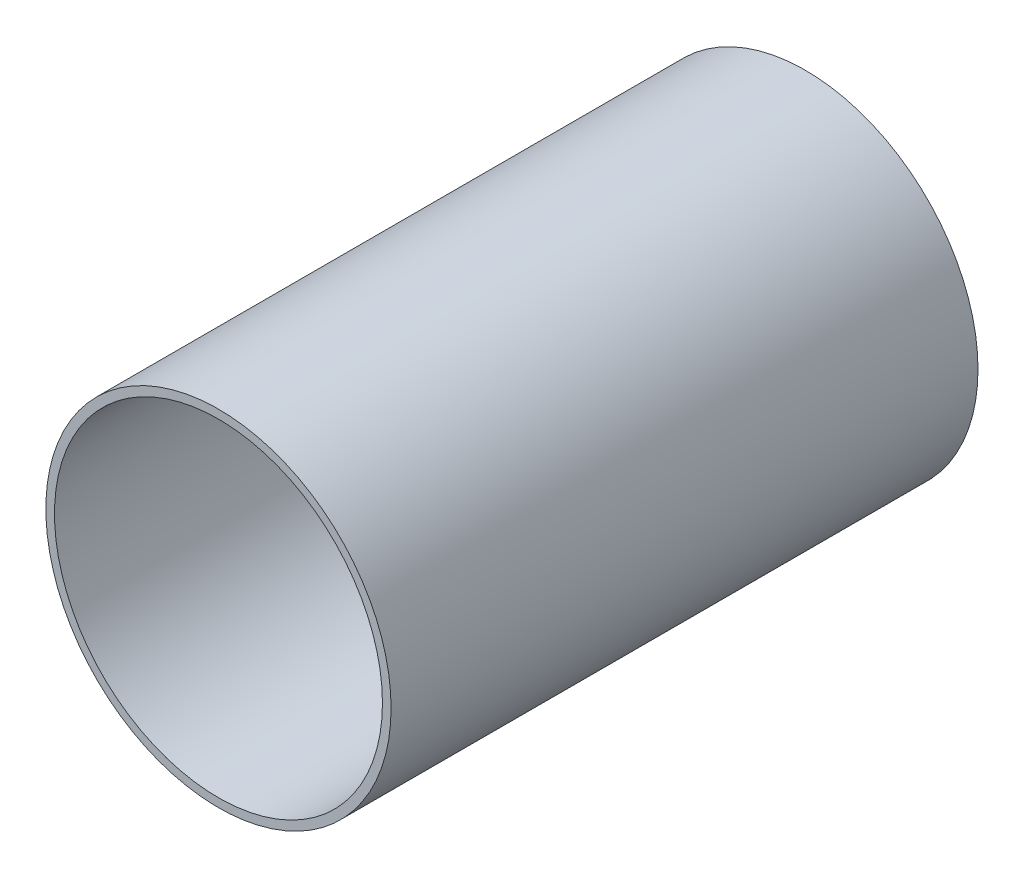
SolidWorks part; units mm, degrees
material "6061-T6 (SS)"
ref_plane "Front Plane" through (0, 0, 0) normal (0, 0, 1) x (1, 0, 0)
ref_plane "Top Plane" through (0, 0, 0) normal (0, 1, 0) x (1, 0, 0)
ref_plane "Right Plane" through (0, 0, 0) normal (1, 0, 0) x (0, 0, -1)
sketch "Sketch1" plane through (0, 0, 0) normal (0, 0, 1) x (1, 0, 0)
  circle A0 centre (0, 0) radius 63.5
  circle A1 centre (0, 0) radius 60.325
  dimension "D1" = 127
  dimension "D2" = 3.175
extrude "Boss-Extrude1" add sketch "Sketch1" along normal mid plane 215.9
